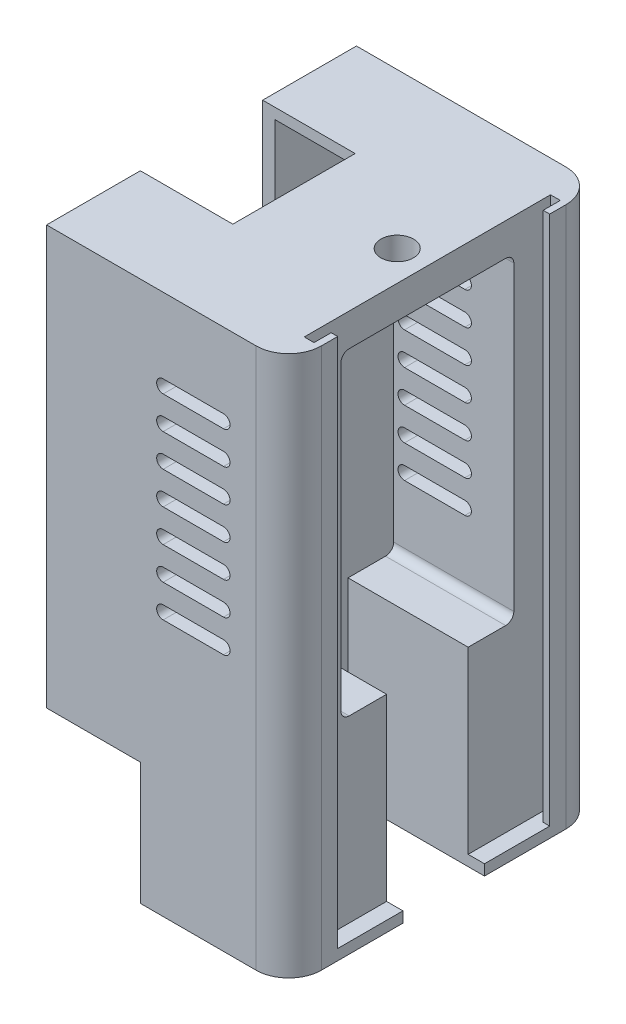
SolidWorks part; units mm, degrees
ref_plane "Front Plane" through (0, 0, 0) normal (0, 0, 1) x (1, 0, 0)
ref_plane "Top Plane" through (0, 0, 0) normal (0, 1, 0) x (1, 0, 0)
ref_plane "Right Plane" through (0, 0, 0) normal (1, 0, 0) x (0, 0, -1)
sketch "Sketch1" plane through (0, 0, 0) normal (0, 0, 1) x (1, 0, 0)
  line L0 (0, 0) -> (37.719, 0)
  line L1 (37.719, 0) -> (37.719, -84.2142)
  line L2 (37.719, -84.2142) -> (0, -84.2142)
  line L3 (0, -84.2142) -> (0, 0)
extrude "Boss-Extrude1" add sketch "Sketch1" against normal blind 46.355 and the other way blind 1.905
sketch "Sketch3" plane through (0, 0, 1.905) normal (0, 0, 1) x (1, 0, 0)
  line L4 (0, -84.2142) -> (14.605, -84.2142)
  line L5 (0, -84.2142) -> (37.719, -84.2142) construction
  line L6 (14.605, -84.2142) -> (14.605, -65.1642)
  line L7 (14.605, -65.1642) -> (0, -65.1642)
  line L8 (0, 0) -> (0, -84.2142) construction
  line L9 (0, -65.1642) -> (0, -84.2142)
extrude "Cut-Extrude1" cut sketch "Sketch3" against normal through all
sketch "Sketch4" plane through (0, 0, 0) normal (0, 1, 0) x (1, 0, 0)
  line L7 (1.905, 22.225) -> (1.905, 31.75)
  line L8 (1.905, 31.75) -> (14.4052, 31.75)
  line L9 (14.4052, 31.75) -> (14.4052, 12.7)
  line L10 (14.4052, 12.7) -> (1.905, 12.7)
  line L11 (1.905, 12.7) -> (1.905, 22.225)
extrude "Cut-Extrude2" cut sketch "Sketch4" along direction (0, 1, 0) on the side against the normal blind 65.405
sketch "Sketch5" plane through (0, 0, 0) normal (-1, 0, 0) x (0, 0, 1)
  line L0 (-22.225, 0) -> (-12.7, 0)
  line L1 (-46.355, 0) -> (1.905, 0) construction
  line L2 (-12.7, 0) -> (-12.7, -38.1)
  line L3 (-12.7, -38.1) -> (-31.75, -38.1)
  line L4 (-31.75, -38.1) -> (-31.75, 0)
  line L5 (-31.75, 0) -> (-22.225, 0)
extrude "Cut-Extrude3" cut sketch "Sketch5" against normal up to next
sketch "Sketch6" plane through (0, -65.1642, 0) normal (0, -1, 0) x (1, 0, 0)
  line L2 (1.905, 0) -> (14.605, 0)
  line L3 (14.605, -46.355) -> (14.605, 1.905) construction
  line L4 (14.605, 0) -> (14.605, -44.45)
  line L5 (14.605, -44.45) -> (1.905, -44.45)
  line L9 (1.905, 0) -> (1.905, -44.45)
extrude "Cut-Extrude4" cut sketch "Sketch6" against normal blind 63.5
sketch "Sketch7" plane through (37.719, 0, 0) normal (1, 0, 0) x (0, 0, -1)
  line L2 (22.225, -5.08) -> (35.687, -5.08)
  line L3 (35.687, -5.08) -> (35.687, -54.61)
  line L4 (35.687, -54.61) -> (28.575, -54.61)
  line L5 (28.575, -54.61) -> (28.575, -84.2142)
  line L6 (-1.905, -84.2142) -> (46.355, -84.2142) construction
  line L7 (28.575, -84.2142) -> (15.875, -84.2142)
  line L8 (15.875, -84.2142) -> (15.875, -54.61)
  line L9 (15.875, -54.61) -> (8.763, -54.61)
  line L10 (8.763, -54.61) -> (8.763, -5.08)
  line L11 (8.763, -5.08) -> (22.225, -5.08)
  point P0 (0, 0)
extrude "Cut-Extrude5" cut sketch "Sketch7" against normal blind 21.2471
sketch "Sketch8" plane through (16.4719, 0, 0) normal (1, 0, 0) x (0, 0, -1)
  circle A0 centre (33.655, -7.62) radius 1.016
  circle A1 centre (10.795, -7.62) radius 1.016
extrude "Boss-Extrude2" add sketch "Sketch8" along normal blind 6.35
fillet "Fillet1" radius 1.27 4 edges at (27.0955, -54.61, -8.763) (27.0955, -54.61, -35.687) (27.0954, -5.08, -8.763) (27.0954, -5.08, -35.687)
sketch "Sketch9" plane through (0, 0, 0) normal (0, 1, 0) x (1, 0, 0)
  line L4 (36.703, 41.402) -> (35.179, 41.402)
  line L5 (35.179, 41.402) -> (35.179, 3.048)
  line L6 (35.179, 3.048) -> (36.703, 3.048)
  line L8 (37.719, -1.905) -> (37.719, 46.355) construction
  line L9 (37.719, 22.225) -> (37.719, 38.735)
  line L10 (37.719, 38.735) -> (36.703, 38.735)
  line L12 (37.719, 22.225) -> (37.719, 5.715)
  line L13 (37.719, 5.715) -> (36.703, 5.715)
  line L14 (36.703, 5.715) -> (36.703, 3.048)
  line L15 (36.703, 41.402) -> (36.703, 38.735)
extrude "Cut-Extrude7" cut sketch "Sketch9" against normal blind 82.55
fillet "Fillet2" radius 5.08 2 edges at (37.719, -42.1071, -46.355) (37.719, -42.1071, 1.905)
sketch "Sketch10" plane through (0, 0, -35.687) normal (0, 0, 1) x (1, 0, 0)
  line L0 (27.559, -12.7) -> (18.161, -12.7) construction
  line L1 (27.559, -17.78) -> (18.161, -17.78) construction
  line L2 (27.559, -13.716) -> (18.161, -13.716)
  line L3 (27.559, -11.684) -> (18.161, -11.684)
  line L4 (27.559, -18.796) -> (18.161, -18.796)
  line L5 (27.559, -16.764) -> (18.161, -16.764)
  line L6 (27.559, -22.86) -> (18.161, -22.86) construction
  line L7 (27.559, -23.876) -> (18.161, -23.876)
  line L8 (27.559, -21.844) -> (18.161, -21.844)
  line L9 (27.559, -27.94) -> (18.161, -27.94) construction
  line L10 (27.559, -28.956) -> (18.161, -28.956)
  line L11 (27.559, -26.924) -> (18.161, -26.924)
  line L12 (27.559, -33.02) -> (18.161, -33.02) construction
  line L13 (27.559, -34.036) -> (18.161, -34.036)
  line L14 (27.559, -32.004) -> (18.161, -32.004)
  line L15 (27.559, -38.1) -> (18.161, -38.1) construction
  line L16 (27.559, -39.116) -> (18.161, -39.116)
  line L17 (27.559, -37.084) -> (18.161, -37.084)
  line L18 (27.559, -43.18) -> (18.161, -43.18) construction
  line L19 (27.559, -44.196) -> (18.161, -44.196)
  line L20 (27.559, -42.164) -> (18.161, -42.164)
  arc A0 (27.559, -13.716) -> (27.559, -11.684) centre (27.559, -12.7) ccw
  arc A1 (18.161, -11.684) -> (18.161, -13.716) centre (18.161, -12.7) ccw
  arc A2 (27.559, -18.796) -> (27.559, -16.764) centre (27.559, -17.78) ccw
  arc A3 (18.161, -16.764) -> (18.161, -18.796) centre (18.161, -17.78) ccw
  arc A4 (27.559, -23.876) -> (27.559, -21.844) centre (27.559, -22.86) ccw
  arc A5 (18.161, -21.844) -> (18.161, -23.876) centre (18.161, -22.86) ccw
  arc A6 (27.559, -28.956) -> (27.559, -26.924) centre (27.559, -27.94) ccw
  arc A7 (18.161, -26.924) -> (18.161, -28.956) centre (18.161, -27.94) ccw
  arc A8 (27.559, -34.036) -> (27.559, -32.004) centre (27.559, -33.02) ccw
  arc A9 (18.161, -32.004) -> (18.161, -34.036) centre (18.161, -33.02) ccw
  arc A10 (27.559, -39.116) -> (27.559, -37.084) centre (27.559, -38.1) ccw
  arc A11 (18.161, -37.084) -> (18.161, -39.116) centre (18.161, -38.1) ccw
  arc A12 (27.559, -44.196) -> (27.559, -42.164) centre (27.559, -43.18) ccw
  arc A13 (18.161, -42.164) -> (18.161, -44.196) centre (18.161, -43.18) ccw
  point P4 (22.86, -12.7)
  point P10 (22.86, -17.78)
  point P17 (22.86, -22.86)
  point P24 (22.86, -27.94)
  point P31 (22.86, -33.02)
  point P38 (22.86, -38.1)
  point P44 (22.86, -43.18)
  point P49 (0, 0)
  point P50 (0, 0)
  dimension "D1" = 7
extrude "Cut-Extrude8" cut sketch "Sketch10" against normal through all and the other way through all
sketch "Sketch12" plane through (0, 0, 0) normal (0, 1, 0) x (1, 0, 0)
  line L0 (35.179, 41.402) -> (35.179, 3.048) construction
  circle A0 centre (30.48, 22.225) radius 2.54
  point P2 (0, 0)
  point P5 (35.179, 22.225)
  point P6 (0, 0)
  point P7 (0, 0)
extrude "Cut-Extrude9" cut sketch "Sketch12" against normal up to next contours A0
